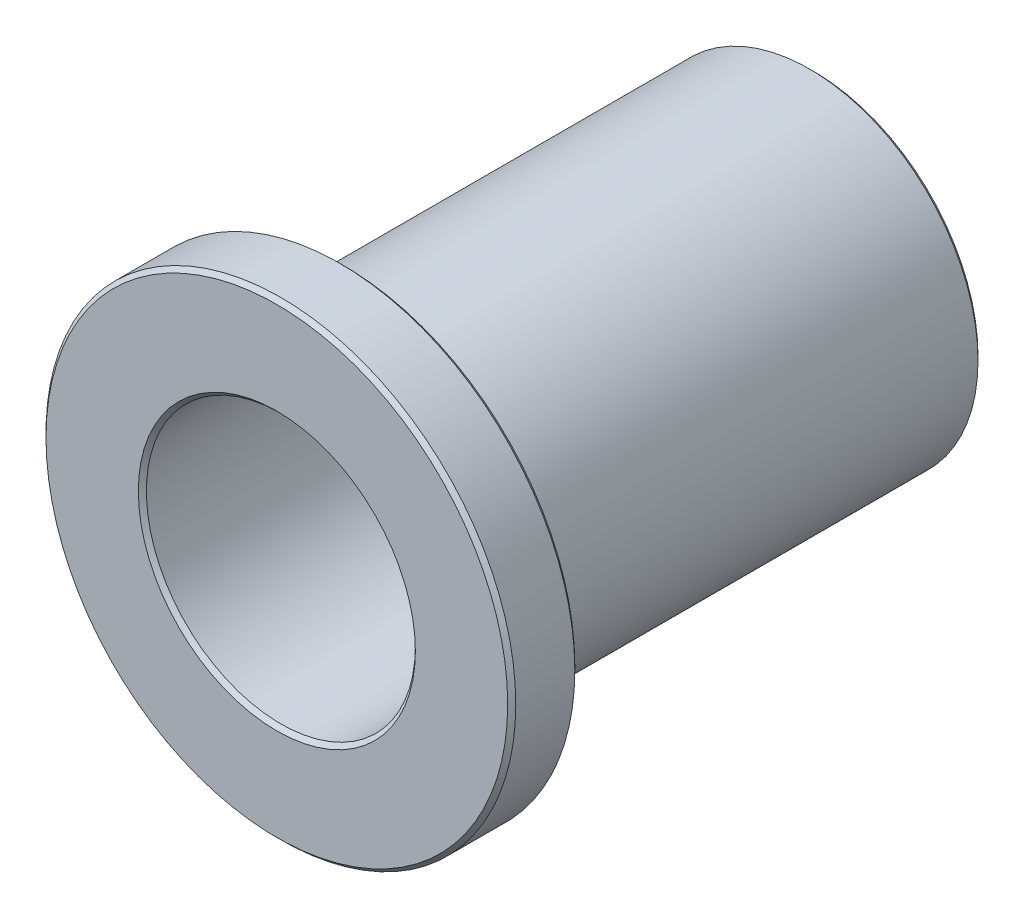
SolidWorks part; units mm, degrees
material "Commercial Bronze, UNS C22000 (90-10 Bronze)"
ref_plane "Front" through (0, 0, 0) normal (0, 0, 1) x (1, 0, 0)
ref_plane "Top" through (0, 0, 0) normal (0, 1, 0) x (1, 0, 0)
ref_plane "Right" through (0, 0, 0) normal (1, 0, 0) x (0, 0, -1)
sketch "Sketch1" plane through (0, 0, 0) normal (0, 0, 1) x (1, 0, 0)
  circle A0 centre (0, 0) radius 6.3627
  circle A1 centre (0, 0) radius 7.9629
  circle A2 centre (0, 0) radius 11.1125
  dimension "ID" = 12.7254
  dimension "OD" = 15.9258
  dimension "Flange OD" = 22.225
sketch "Sketch2" plane through (0, 0, 0) normal (1, 0, 0) x (0, 0, -1)
  line L0 (-12.7, -11.1125) -> (12.7, -11.1125) construction
  line L1 (0, 11.1125) -> (0, -11.1125) construction
  line L3 (-9.525, 7.9629) -> (12.7, 7.9629) construction
  point P3 (0, -11.1125)
  point P7 (0, 7.9629)
  point P9 (-9.525, -11.1125)
  point P10 (-12.7, 11.1125)
  point P23 (0, 11.1125)
  dimension "Flange Thickness" = 3.175
  dimension "Length" = 25.4
sketch "Sketch3" plane through (0, 0, 0) normal (0, 0, 1) x (1, 0, 0)
  circle A0 centre (0, 0) radius 11.1125 construction
  circle A1 centre (0, 0) radius 11.1125
  circle A2 centre (0, 0) radius 6.3627 construction
  circle A3 centre (0, 0) radius 6.3627
extrude "Boss-Extrude1" add sketch "Sketch3" against normal up to vertex (-9.525 mm away) from vertex at 12.7 starting at point (0, -11.1125, 12.7)
sketch "Sketch4" plane through (0, 0, 0) normal (0, 0, 1) x (1, 0, 0)
  circle A0 centre (0, 0) radius 6.3627 construction
  circle A1 centre (0, 0) radius 7.9629 construction
  circle A2 centre (0, 0) radius 6.3627
  circle A3 centre (0, 0) radius 7.9629
extrude "Boss-Extrude2" add sketch "Sketch4" against normal up to vertex (12.7 mm away) from vertex at 9.525 starting at point (0, -11.1125, 9.525)
chamfer "Chamfer1" distance 0.1909 angle 45 6 edges at (6.3627, 0, 12.7) (11.1125, 0, 12.7) (11.1125, 0, 9.525) (7.9629, 0, 9.525) (6.3627, 0, -12.7) (7.9629, 0, -12.7)
equation "\"D1@Chamfer1\"=\"ID@Sketch1\"*0.015"
